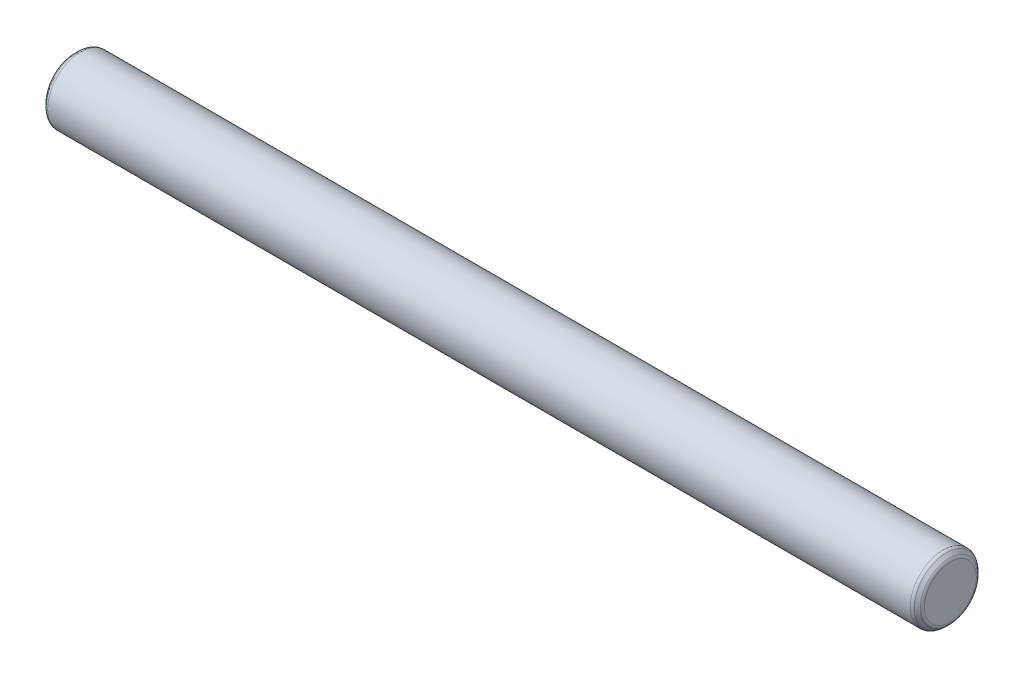
SolidWorks part; units mm, degrees
ref_plane "Front Plane" through (0, 0, 0) normal (0, 0, 1) x (1, 0, 0)
ref_plane "Top Plane" through (0, 0, 0) normal (0, 1, 0) x (1, 0, 0)
ref_plane "Right Plane" through (0, 0, 0) normal (1, 0, 0) x (0, 0, -1)
sketch "Sketch1" plane through (0, 0, 0) normal (1, 0, 0) x (0, 0, -1)
  circle A0 centre (0, 0) radius 3.1115
  dimension "D1" = 6.223
extrude "Boss-Extrude1" add sketch "Sketch1" along normal blind 82.55
chamfer "Chamfer1" distance 0.508 angle 45 2 edges at (82.55, 0, -3.1115) (0, 0, -3.1115)
fillet "Fillet1" radius 0.381 4 edges at (82.55, 0, -2.6035) (82.042, 0, -3.1115) (0.508, 0, -3.1115) (0, 0, -2.6035)
